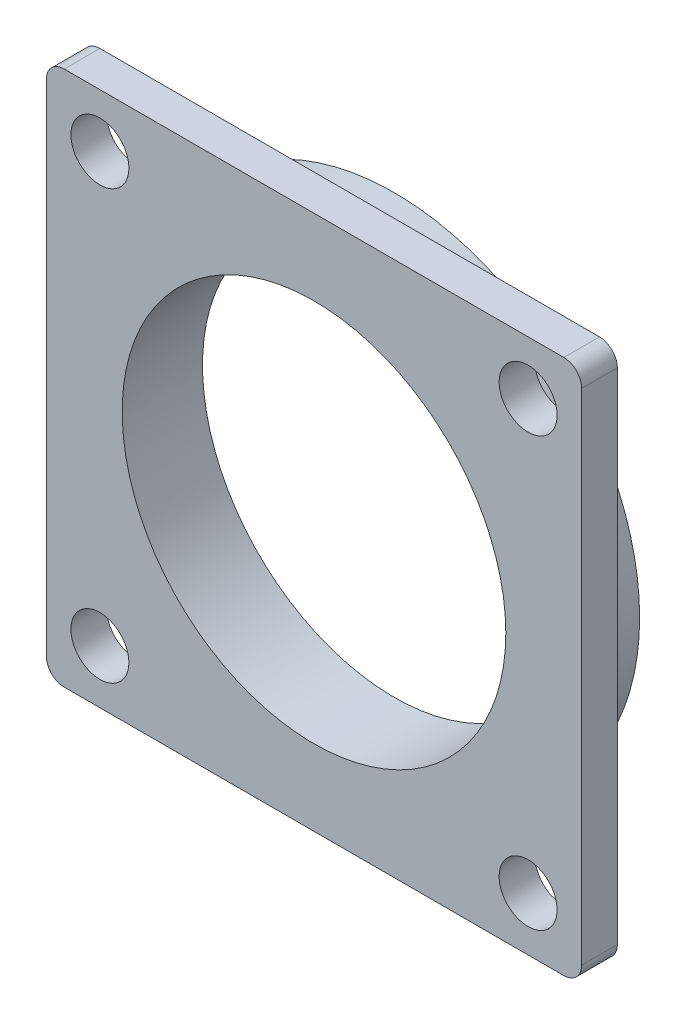
SolidWorks part; units mm, degrees
ref_plane "Plan de face" through (0, 0, 0) normal (0, 0, 1) x (1, 0, 0)
ref_plane "Plan de dessus" through (0, 0, 0) normal (0, 1, 0) x (1, 0, 0)
ref_plane "Plan de droite" through (0, 0, 0) normal (1, 0, 0) x (0, 0, -1)
sketch "Esquisse1" plane through (0, 0, 0) normal (0, 0, 1) x (1, 0, 0)
  circle A0 centre (24.9946, -11.6314) radius 10.75
  circle A1 centre (24.9946, -11.6314) radius 13.75
  dimension "D1" = 21.5
  dimension "D2" = 27.5
extrude "Boss.-Extru.1" add sketch "Esquisse1" along normal blind 2.5
sketch "Esquisse2" plane through (0, 0, 2.5) normal (0, 0, 1) x (1, 0, 0)
  line L1 (9.9946, 3.3686) -> (39.9946, 3.3686)
  line L2 (9.9946, 3.3686) -> (9.9946, -26.6314)
  line L3 (9.9946, -26.6314) -> (39.9946, -26.6314)
  line L4 (39.9946, 3.3686) -> (39.9946, -26.6314)
  circle A0 centre (12.9946, 0.3686) radius 1.625
  circle A1 centre (36.9946, 0.3686) radius 1.625
  circle A2 centre (12.9946, -23.6314) radius 1.625
  circle A3 centre (36.9946, -23.6314) radius 1.625
  circle A4 centre (24.9946, -11.6314) radius 10.75 construction
  point P14 (29.8914, 8.9209)
  point P15 (28.9581, -13.0951)
  point P18 (13.9249, -13.8433)
  dimension "D9" = 3.25
  dimension "D10" = 3.25
  dimension "D11" = 3.25
  dimension "D12" = 3.25
  dimension "D13" = 12
  dimension "D1" = 30
  dimension "D2" = 30
  dimension "D3" = 24
  dimension "D4" = 24
  dimension "D5" = 24
  dimension "D6" = 24
  dimension "D7" = 24
  dimension "D8" = 24
  dimension "D14" = 12
  dimension "D15" = 3
  dimension "D16" = 3
extrude "Boss.-Extru.2" add sketch "Esquisse2" along normal blind 2
sketch "Esquisse3" plane through (0, 0, 0) normal (0, 0, -1) x (-1, 0, 0)
  circle A0 centre (-24.9946, -11.6314) radius 10.75
  dimension "D1" = 21.5
extrude "Enlèv. mat.-Extru.1" cut sketch "Esquisse3" against normal blind 23
fillet "Congé1" radius 1 4 edges at (9.9946, -26.6314, 3.5) (39.9946, -26.6314, 3.5) (9.9946, 3.3686, 3.5) (39.9946, 3.3686, 3.5)
